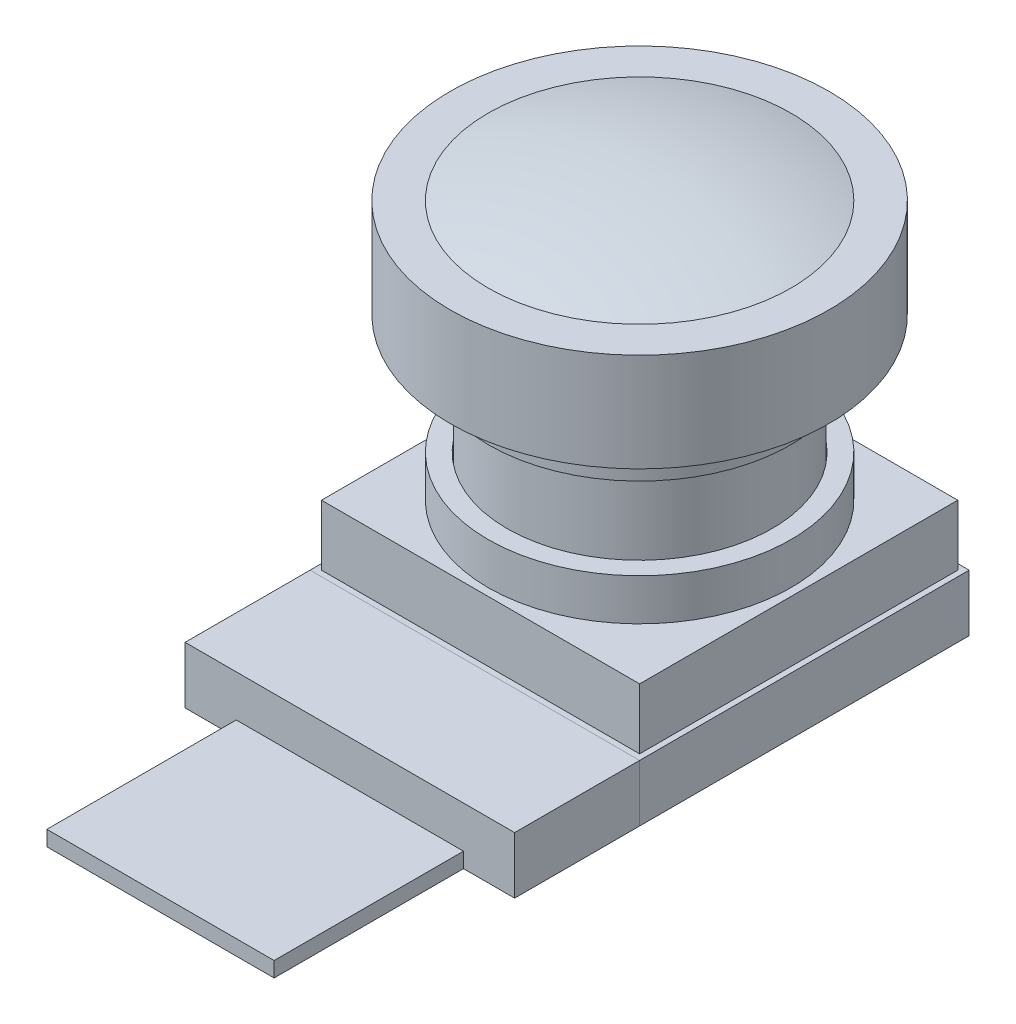
SolidWorks part; units mm, degrees
material "ABS"
ref_plane "前视基准面" through (0, 0, 0) normal (0, 0, 1) x (1, 0, 0)
ref_plane "上视基准面" through (0, 0, 0) normal (0, 1, 0) x (1, 0, 0)
ref_plane "右视基准面" through (0, 0, 0) normal (1, 0, 0) x (0, 0, -1)
other "Configuration Table"
sketch "草图1" plane through (0, 0, 0) normal (0, 1, 0) x (1, 0, 0)
  line L1 (-4.35, 4.35) -> (4.35, 4.35)
  line L2 (-4.35, 4.35) -> (-4.35, -4.35)
  line L3 (-4.35, -4.35) -> (4.35, -4.35)
  line L4 (4.35, 4.35) -> (4.35, -4.35)
  line L5 (-4.35, 4.35) -> (4.35, -4.35) construction
  line L6 (-4.35, -4.35) -> (4.35, 4.35) construction
  point P0 (0, 0)
  dimension "D1" = 8.7
extrude "凸台-拉伸1" add sketch "草图1" along normal blind 3.1
sketch "草图2" plane through (0, 3.1, 0) normal (0, 1, 0) x (1, 0, 0)
  circle A0 centre (0, 0) radius 4
  circle A1 centre (0, 0) radius 3.5
  dimension "D1" = 8
  dimension "D2" = 7
extrude "凸台-拉伸2" add sketch "草图2" along normal blind 1.1
sketch "草图3" plane through (0, 3.1, 0) normal (0, 1, 0) x (1, 0, 0)
  circle A0 centre (0, 0) radius 3.48
  circle A1 centre (0, 0) radius 3.5 construction
  dimension "D1" = 0.02
extrude "凸台-拉伸3" add sketch "草图3" along normal offset from surface (6.85 mm away) 9.95 up to face at (0, 0, 0)
sketch "草图4" plane through (0, 9.95, 0) normal (0, 1, 0) x (1, 0, 0)
  circle A0 centre (0, 0) radius 5
  dimension "D1" = 10
extrude "凸台-拉伸4" add sketch "草图4" against normal blind 2.6
sketch "草图5" plane through (0, 0, 4.35) normal (0, 0, 1) x (1, 0, 0)
  line L0 (4.35, 3.1) -> (4.35, 0) construction
  line L1 (-4.35, 0) -> (4.35, 0)
  line L2 (-4.35, 0) -> (-4.35, 1.5)
  line L3 (-4.35, 1.5) -> (4.35, 1.5)
  line L4 (4.35, 0) -> (4.35, 1.5)
  dimension "D1" = 1.5
extrude "凸台-拉伸5" add sketch "草图5" along normal blind 3.3 separate body
sketch "草图10" plane through (0, 0, 0) normal (0, 1, 0) x (1, 0, 0)
  line L0 (4.35, -7.65) -> (-4.35, -7.65) construction
  line L1 (-3, -7.65) -> (3, -7.65)
  line L2 (-3, -7.65) -> (-3, -12.65)
  line L3 (-3, -12.65) -> (3, -12.65)
  line L4 (3, -7.65) -> (3, -12.65)
  point P6 (0, -7.65)
  dimension "D1" = 5
  dimension "D2" = 6
extrude "凸台-拉伸6" add sketch "草图10" along normal blind 0.4 separate body
sketch "草图13" plane through (0, 3.1, 0) normal (0, 1, 0) x (1, 0, 0)
  line L1 (-4.2, 4.2) -> (4.2, 4.2)
  line L2 (-4.2, 4.2) -> (-4.2, -4.2)
  line L3 (-4.2, -4.2) -> (4.2, -4.2)
  line L4 (4.35, -4.35) -> (4.35, 4.35)
  line L5 (4.35, 4.35) -> (-4.35, 4.35)
  line L8 (4.35, -4.35) -> (4.35, 4.35)
  line L12 (4.2, 4.2) -> (4.2, -4.2)
  line L13 (-4.2, 4.2) -> (4.2, -4.2) construction
  line L14 (-4.2, -4.2) -> (4.2, 4.2) construction
  line L17 (4.35, 4.35) -> (-4.35, 4.35)
  line L18 (-4.35, 4.35) -> (-4.35, -4.35)
  line L19 (-4.35, 4.35) -> (-4.35, -4.35)
  line L20 (-4.35, -4.35) -> (4.35, -4.35)
  line L21 (-4.35, -4.35) -> (4.35, -4.35)
  point P2 (0, 0)
  dimension "D2" = 0.15
  dimension "D1" = 0
extrude "切除-拉伸1" cut sketch "草图13" against normal up to surface (1.6 mm away) up to face at (0, 1.5, 6)
sketch "草图14" plane through (0, 7.35, 0) normal (0, -1, 0) x (1, 0, 0)
  circle A0 centre (0, 0) radius 3.48 construction
  circle A1 centre (0, 0) radius 3.48
  circle A2 centre (0, 0) radius 3.98
  dimension "D1" = 0.5
extrude "凸台-拉伸7" add sketch "草图14" along normal blind 1
sketch "草图11" plane through (0, 0, 0) normal (0, 0, 1) x (1, 0, 0)
  line L0 (0, 9.95) -> (0, 0) construction
  line L1 (5, 9.95) -> (-5, 9.95) construction
  line L2 (0, 9.95) -> (-4, 9.95)
  line L4 (0, 9.95) -> (0, 10.55)
  line L5 (0, 7.35) -> (0, 9.95) construction
  line L6 (-5, 9.95) -> (-5, 7.35) construction
  line L7 (-3, 0) -> (3, 0) construction
  arc A0 (-4, 9.95) -> (0, 10.55) centre (0, -3.0833) cw
  dimension "D1" = 0.6
  dimension "D2" = 1
revolve "旋转3" add sketch "草图11" angle 360 about L0
